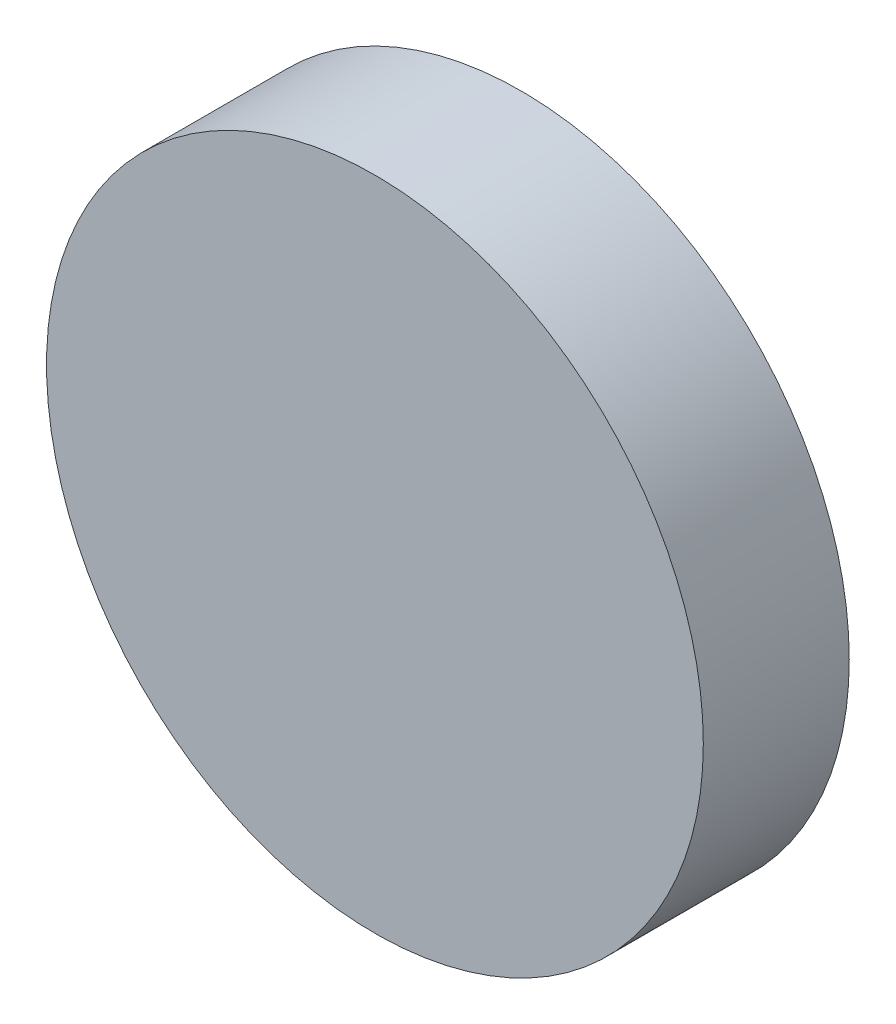
SolidWorks part; units mm, degrees
ref_plane "Front Plane" through (0, 0, 0) normal (0, 0, 1) x (1, 0, 0)
ref_plane "Top Plane" through (0, 0, 0) normal (0, 1, 0) x (1, 0, 0)
ref_plane "Right Plane" through (0, 0, 0) normal (1, 0, 0) x (0, 0, -1)
sketch "Sketch2" plane through (0, 0, 0) normal (0, 0, 1) x (1, 0, 0)
  circle A0 centre (0, 0) radius 11.43
  dimension "D1" = 22.86
extrude "Boss-Extrude1" add sketch "Sketch2" along normal blind 5.08
